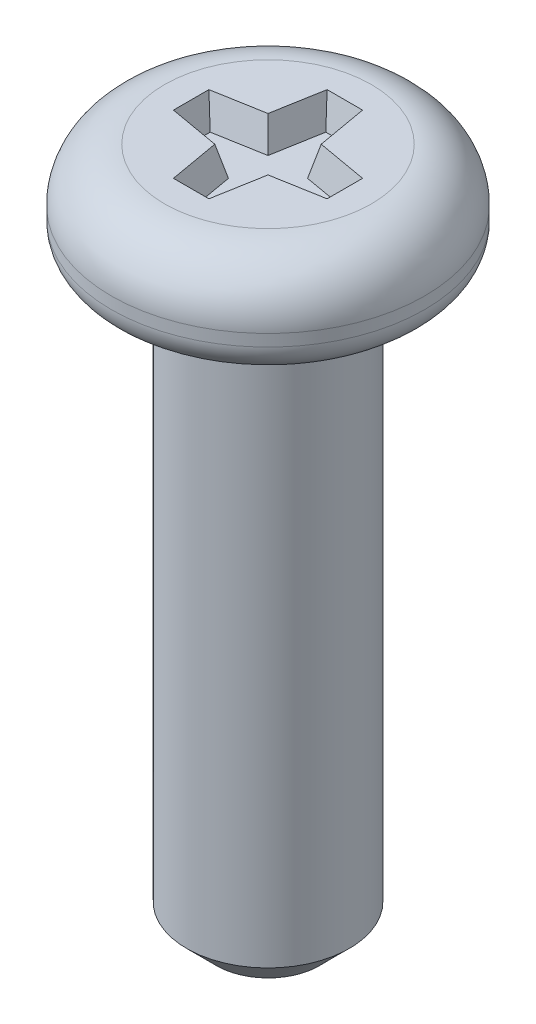
SolidWorks part; units mm, degrees
ref_plane "Front Plane" through (0, 0, 0) normal (0, 0, 1) x (1, 0, 0)
ref_plane "Top Plane" through (0, 0, 0) normal (0, 1, 0) x (1, 0, 0)
ref_plane "Right Plane" through (0, 0, 0) normal (1, 0, 0) x (0, 0, -1)
sketch "Sketch1" plane through (0, 0, 0) normal (0, 0, 1) x (1, 0, 0)
  line L0 (0, 0) -> (0, -11.6) construction
  line L1 (0, -11.6) -> (0.875, -11.6)
  line L2 (1.375, -11.1) -> (1.375, -1.75)
  line L3 (1.525, -1.6) -> (2.15, -1.6)
  line L4 (2.65, -1.1) -> (2.65, -0.9)
  line L5 (1.75, 0) -> (0, 0)
  line L6 (0, 0) -> (0, -11.6)
  line L7 (1.375, -11.1) -> (0.875, -11.6)
  arc A0 (2.65, -0.9) -> (1.75, 0) centre (1.75, -0.9) ccw
  arc A1 (2.15, -1.6) -> (2.65, -1.1) centre (2.15, -1.1) ccw
  arc A2 (1.375, -1.75) -> (1.525, -1.6) centre (1.525, -1.75) cw
  point P3 (0.8068, -9.6)
  point P13 (1.375, -1.6)
  point P14 (0.992, -9.6)
  dimension "D3" = 0.9
  dimension "D6" = 0.5
  dimension "D7" = 0.15
  dimension "D8" = 135
  dimension "D4" = 0.5
  dimension "D1" = 5.3
  dimension "D2" = 1.6
  dimension "D5" = 2.75
  dimension "D9" = 10
revolve "Revolve1" add sketch "Sketch1" angle 360 about L0
sketch "Sketch2" plane through (0, 0, 0) normal (0, 1, 0) x (1, 0, 0)
  line L0 (0, 1.3) -> (0, 0) construction
  line L1 (0, 0) -> (1.3, 0) construction
  line L2 (-0.3001, 1.3) -> (0.3001, 1.3)
  line L3 (0.3001, 1.3) -> (0.45, 0.45)
  line L4 (0.45, 0.45) -> (1.3, 0.3001)
  line L5 (1.3, 0.3001) -> (1.3, -0.3001)
  line L6 (-1.3, 0.3001) -> (-1.3, -0.3001)
  line L7 (-0.45, 0.45) -> (-1.3, 0.3001)
  line L8 (-0.3001, 1.3) -> (-0.45, 0.45)
  line L9 (-0.45, -0.45) -> (-1.3, -0.3001)
  line L10 (-0.3001, -1.3) -> (-0.45, -0.45)
  line L11 (-0.3001, -1.3) -> (0.3001, -1.3)
  line L12 (0.3001, -1.3) -> (0.45, -0.45)
  line L13 (0.45, -0.45) -> (1.3, -0.3001)
  point P18 (-1.3, 0)
  point P26 (0, 0)
  dimension "D1" = 100
  dimension "D2" = 2.6
  dimension "D3" = 0.9
extrude "Cut-Extrude1" cut sketch "Sketch2" against normal blind 0.5 draft 15
